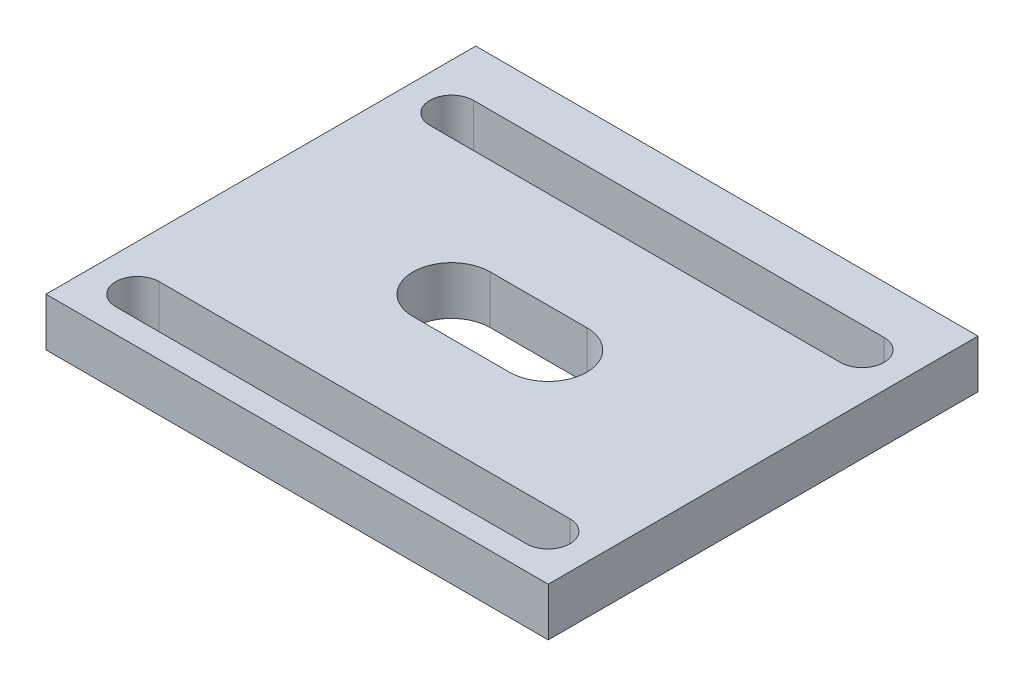
SolidWorks part; units mm, degrees
ref_plane "Front Plane" through (0, 0, 0) normal (0, 0, 1) x (1, 0, 0)
ref_plane "Top Plane" through (0, 0, 0) normal (0, 1, 0) x (1, 0, 0)
ref_plane "Right Plane" through (0, 0, 0) normal (1, 0, 0) x (0, 0, -1)
sketch "Sketch1" plane through (0, 0, 0) normal (0, 1, 0) x (1, 0, 0)
  line L0 (-25.3732, 1.3734) -> (-25.3732, -2.6468) construction
  line L6 (-57.3732, 17.3532) -> (-57.3732, -35.6468)
  line L7 (92.6268, 29.3532) -> (92.6268, -35.6468)
  line L8 (58.6268, 31.3532) -> (58.6268, -35.6468) construction
  line L11 (58.6268, -2.1468) -> (37.6268, -2.1468) construction
  line L14 (37.6268, 18.8532) -> (79.6268, 18.8532) construction
  line L17 (37.6268, 18.8532) -> (37.6268, -23.1468) construction
  line L26 (37.6268, -23.1468) -> (79.6268, -23.1468) construction
  line L27 (79.6268, 18.8532) -> (79.6268, -23.1468) construction
  line L28 (37.6268, 18.8532) -> (79.6268, -23.1468) construction
  line L29 (37.6268, -23.1468) -> (79.6268, 18.8532) construction
  line L32 (32.3633, 14.1166) -> (74.8902, 14.1166) construction
  line L35 (32.3633, 16.3666) -> (74.8902, 16.3666)
  line L46 (32.3633, 11.8666) -> (74.8902, 11.8666)
  line L49 (32.3633, -18.4103) -> (74.8902, -18.4103) construction
  line L62 (90.6268, 31.3532) -> (26.6268, 31.3532)
  line L63 (32.3633, -20.6603) -> (74.8902, -20.6603)
  line L64 (32.3633, -16.1603) -> (74.8902, -16.1603)
  line L65 (48.6268, -2.1468) -> (58.6268, -2.1468) construction
  line L66 (48.6268, 1.8532) -> (58.6268, 1.8532)
  line L67 (48.6268, -6.1468) -> (58.6268, -6.1468)
  line L68 (26.6268, 31.3532) -> (-57.3732, 31.3532)
  line L69 (-57.3732, 31.3532) -> (-57.3732, 17.3532)
  line L72 (-57.3732, -35.6468) -> (-57.3732, -43.6468)
  line L73 (-57.3732, -43.6468) -> (92.6268, -43.6468)
  line L74 (92.6268, -35.6468) -> (92.6268, -43.6468)
  arc A27 (92.6268, 29.3532) -> (90.6268, 31.3532) centre (90.6268, 29.3532) ccw
  circle A29 centre (-25.3732, -2.6468) radius 4
  circle A31 centre (58.6268, -2.1468) radius 33.5 construction
  arc A34 (32.3633, 16.3666) -> (32.3633, 11.8666) centre (32.3633, 14.1166) ccw
  arc A35 (74.8902, 11.8666) -> (74.8902, 16.3666) centre (74.8902, 14.1166) ccw
  arc A36 (32.3633, -20.6603) -> (32.3633, -16.1603) centre (32.3633, -18.4103) cw
  arc A37 (74.8902, -16.1603) -> (74.8902, -20.6603) centre (74.8902, -18.4103) cw
  arc A38 (48.6268, 1.8532) -> (48.6268, -6.1468) centre (48.6268, -2.1468) ccw
  arc A39 (58.6268, -6.1468) -> (58.6268, 1.8532) centre (58.6268, -2.1468) ccw
  point P0 (0, 0)
  point P4 (58.6268, -2.1468)
  point P13 (-13.2549, 19.3532)
  point P14 (53.6268, -18.4103)
  point P16 (32.3633, 14.1166)
  point P18 (53.6268, 14.1166)
  point P30 (48.6268, -2.1468)
  point P32 (53.6268, -2.1468)
  point P79 (-37.1485, 19.3879)
  point P104 (92.6268, 31.3532)
  dimension "D4" = 8
  dimension "D5" = 34
  dimension "D7" = 42
  dimension "D8" = 42
  dimension "D13" = 4
  dimension "D14" = 2.25
  dimension "D27" = 2
  dimension "D9" = 33.5
  dimension "D10" = 32
  dimension "D11" = 10
  dimension "D32" = 150
extrude "Boss-Extrude1" add sketch "Sketch1" along normal blind 5
sketch "Sketch2" plane through (0, 5, 0) normal (0, 1, 0) x (1, 0, 0)
  line L0 (-25.3732, -2.6468) -> (-25.3732, 14.3532) construction
  line L1 (-40.3732, 12.3532) -> (-10.3732, 12.3532) construction
  line L2 (-40.3732, 12.3532) -> (-40.3732, -17.6468) construction
  line L3 (-40.3732, -17.6468) -> (-10.3732, -17.6468) construction
  line L4 (-10.3732, 12.3532) -> (-10.3732, -17.6468) construction
  line L5 (-40.3732, 12.3532) -> (-10.3732, -17.6468) construction
  line L6 (-40.3732, -17.6468) -> (-10.3732, 12.3532) construction
  line L7 (-25.3732, -2.6468) -> (-42.3732, -2.6468) construction
  line L8 (-47.394, 9.374) -> (-13.3524, 9.374) construction
  line L9 (-47.394, 11.624) -> (-13.3524, 11.624)
  line L10 (-47.394, 7.124) -> (-13.3524, 7.124)
  line L11 (-47.394, -14.6676) -> (-13.3524, -14.6676) construction
  line L12 (-47.394, -16.9176) -> (-13.3524, -16.9176)
  line L13 (-47.394, -12.4176) -> (-13.3524, -12.4176)
  line L14 (-35.3732, -2.6468) -> (-25.3732, -2.6468) construction
  line L15 (-35.3732, 1.3532) -> (-25.3732, 1.3532)
  line L16 (-35.3732, -6.6468) -> (-25.3732, -6.6468)
  circle A0 centre (-25.3732, -2.6468) radius 17 construction
  circle A1 centre (-37.394, 9.374) radius 2.25 construction
  circle A2 centre (-13.3524, 9.374) radius 2.25 construction
  circle A3 centre (-13.3524, -14.6676) radius 2.25 construction
  circle A4 centre (-37.394, -14.6676) radius 2.25 construction
  arc A5 (-47.394, 11.624) -> (-47.394, 7.124) centre (-47.394, 9.374) ccw
  arc A6 (-13.3524, 7.124) -> (-13.3524, 11.624) centre (-13.3524, 9.374) ccw
  arc A7 (-47.394, -16.9176) -> (-47.394, -12.4176) centre (-47.394, -14.6676) cw
  arc A8 (-13.3524, -12.4176) -> (-13.3524, -16.9176) centre (-13.3524, -14.6676) cw
  arc A9 (-35.3732, 1.3532) -> (-35.3732, -6.6468) centre (-35.3732, -2.6468) ccw
  arc A10 (-25.3732, -6.6468) -> (-25.3732, 1.3532) centre (-25.3732, -2.6468) ccw
  point P0 (-25.3732, -2.6468)
  point P18 (-35.3732, -2.6468)
  point P19 (-47.394, 9.374)
  point P21 (-30.3732, 9.374)
  point P27 (-30.3732, -14.6676)
  point P33 (-30.3732, -2.6468)
  dimension "D3" = 17
  dimension "D4" = 10
  dimension "D6" = 2.25
  dimension "D7" = 4
  dimension "D1" = 30
  dimension "D2" = 30
  dimension "D5" = 10
extrude "Cut-Extrude1" cut sketch "Sketch2" against normal blind 10
sketch "Sketch3" plane through (0, 5, 0) normal (0, 1, 0) x (1, 0, 0)
  line L2 (17.7494, 19.0897) -> (17.7494, -35.6468) construction
  line L4 (17.7494, 13.3532) -> (17.7494, 3.3532) construction
  line L5 (21.7494, 13.3532) -> (21.7494, 3.3532)
  line L6 (13.7494, 13.3532) -> (13.7494, 3.3532)
  line L7 (17.7494, -14.6468) -> (17.7494, -24.6468) construction
  line L8 (21.7494, -14.6468) -> (21.7494, -24.6468)
  line L9 (13.7494, -14.6468) -> (13.7494, -24.6468)
  line L11 (90.6268, 31.3532) -> (-57.3732, 31.3532) construction
  arc A0 (21.7494, 13.3532) -> (13.7494, 13.3532) centre (17.7494, 13.3532) ccw
  arc A1 (13.7494, 3.3532) -> (21.7494, 3.3532) centre (17.7494, 3.3532) ccw
  arc A2 (21.7494, -14.6468) -> (13.7494, -14.6468) centre (17.7494, -14.6468) ccw
  arc A3 (13.7494, -24.6468) -> (21.7494, -24.6468) centre (17.7494, -24.6468) ccw
  point P0 (17.7494, 19.0897)
  point P11 (17.7494, 8.3532)
  point P16 (17.7494, -19.6468)
  point P17 (-13.3524, 9.374)
  point P26 (-13.3524, -14.6676)
  dimension "D3" = 4
  dimension "D4" = 4
  dimension "D1" = 18
  dimension "D2" = 10
  dimension "D5" = 10
  dimension "D6" = 31.1018
  dimension "D7" = 28
extrude "Cut-Extrude2" cut sketch "Sketch3" against normal blind 10
sketch "Sketch5" plane through (0, 0, 43.6468) normal (0, 0, 1) x (1, 0, 0)
  line L0 (-57.3732, 2.5) -> (92.6268, 2.5) construction
  line L3 (17.6268, 0) -> (17.6268, 5) construction
  circle A0 centre (-47.3732, 2.5) radius 1.6
  circle A1 centre (82.6268, 2.5) radius 1.6
  point P6 (-47.3732, 2.5)
  dimension "D1" = 10
extrude "Cut-Extrude5" cut sketch "Sketch5" along normal blind 10 from surface at -75 contours A0 | A1 starting at face at (16.6268, 2.5, -31.3532)
sketch "Sketch6" plane through (0, 5, 0) normal (0, 1, 0) x (1, 0, 0)
  line L0 (90.6268, 31.3532) -> (-57.3732, 31.3532) construction
  line L1 (92.6268, -43.6468) -> (92.6268, 29.3532) construction
  line L3 (27.6268, 31.3532) -> (-57.3732, 31.3532)
  line L4 (27.6268, 31.3532) -> (27.6268, -43.6468)
  line L5 (27.6268, -43.6468) -> (-57.3732, -43.6468)
  line L6 (-57.3732, 31.3532) -> (-57.3732, -43.6468)
  point P0 (27.6268, 31.3532)
  dimension "D1" = 65
extrude "Cut-Extrude6" cut sketch "Sketch6" against normal blind 10
sketch "Sketch7" plane through (0, 5, 0) normal (0, 1, 0) x (1, 0, 0)
  line L0 (27.6268, -43.6468) -> (27.6268, 31.3532) construction
  line L1 (27.6268, -28.6468) -> (92.6268, -28.6468)
  line L2 (92.6268, -43.6468) -> (92.6268, 29.3532) construction
  line L4 (27.6268, -28.6468) -> (92.6268, -28.6468)
  line L5 (27.6268, -28.6468) -> (27.6268, -43.6468)
  line L6 (27.6268, -43.6468) -> (92.6268, -43.6468)
  line L7 (92.6268, -28.6468) -> (92.6268, -43.6468)
  point P0 (27.6268, -28.6468)
  line M5 (27.6268, 31.3532) -> (27.6268, -43.6468)
  line M6 (27.6268, -43.6468) -> (92.6268, -43.6468)
  line M7 (92.6268, -43.6468) -> (92.6268, 29.3532)
  dimension "D1" = 15
extrude "Cut-Extrude7" cut sketch "Sketch7" against normal blind 10 contours L1 M5 M6 M7
sketch "Sketch8" plane through (0, 5, 0) normal (0, 1, 0) x (1, 0, 0)
  line L0 (27.6268, -28.6468) -> (27.6268, 31.3532) construction
  line L1 (92.6268, -28.6468) -> (92.6268, 29.3532) construction
  line L2 (27.6268, 31.3532) -> (92.6268, 31.3532)
  line L3 (27.6268, 31.3532) -> (27.6268, 21.3532)
  line L4 (27.6268, 21.3532) -> (92.6268, 21.3532)
  line L5 (92.6268, 31.3532) -> (92.6268, 21.3532)
  line L6 (27.6268, -28.6468) -> (92.6268, -28.6468) construction
  line L7 (92.6268, 21.3532) -> (79.6402, 21.3532)
  line L8 (92.6268, 21.3532) -> (92.6268, -28.6468)
  line L9 (92.6268, -28.6468) -> (79.6402, -28.6468)
  line L10 (79.6402, 21.3532) -> (79.6402, -28.6468)
  arc A0 (32.3633, 16.3666) -> (32.3633, 11.8666) centre (32.3633, 14.1166) ccw construction
  arc A1 (74.8902, 11.8666) -> (74.8902, 16.3666) centre (74.8902, 14.1166) ccw construction
  point P0 (27.6268, 21.3532)
  point P10 (30.1133, 14.1166)
  point P11 (77.1402, 14.1166)
  point P15 (79.6402, 14.1166)
  line M17 (27.6268, 31.3532) -> (27.6268, -28.6468)
  line M18 (27.6268, -28.6468) -> (92.6268, -28.6468)
  line M19 (92.6268, -28.6468) -> (92.6268, 29.3532)
  arc M20 (92.6268, 29.3532) -> (90.6268, 31.3532) centre (90.6268, 29.3532) ccw
  line M21 (90.6268, 31.3532) -> (27.6268, 31.3532)
  dimension "D1" = 10
  dimension "D2" = 2.5
extrude "Cut-Extrude8" cut sketch "Sketch8" against normal blind 10 contours L4 M17 M19 M20 M21 | L4 L10 M18 M19
sketch "Sketch9" plane through (0, 5, 0) normal (0, 1, 0) x (1, 0, 0)
  line L0 (27.6268, -28.6468) -> (27.6268, 21.3532) construction
  line L1 (27.6268, -23.1468) -> (79.6402, -23.1468)
  line L2 (79.6402, 21.3532) -> (79.6402, -28.6468) construction
  line L4 (27.6268, -23.1468) -> (79.6402, -23.1468)
  line L5 (27.6268, -23.1468) -> (27.6268, -28.6468)
  line L6 (27.6268, -28.6468) -> (79.6402, -28.6468)
  line L7 (79.6402, -23.1468) -> (79.6402, -28.6468)
  point P0 (27.6268, -23.1468)
  line M5 (79.6402, -28.6468) -> (79.6402, 21.3532)
  line M7 (27.6268, 21.3532) -> (27.6268, -28.6468)
  line M8 (27.6268, -28.6468) -> (79.6402, -28.6468)
  dimension "D1" = 5.5
extrude "Cut-Extrude9" cut sketch "Sketch9" against normal blind 10 contours L1 M7 M8 M5 | L7 L6 L5
